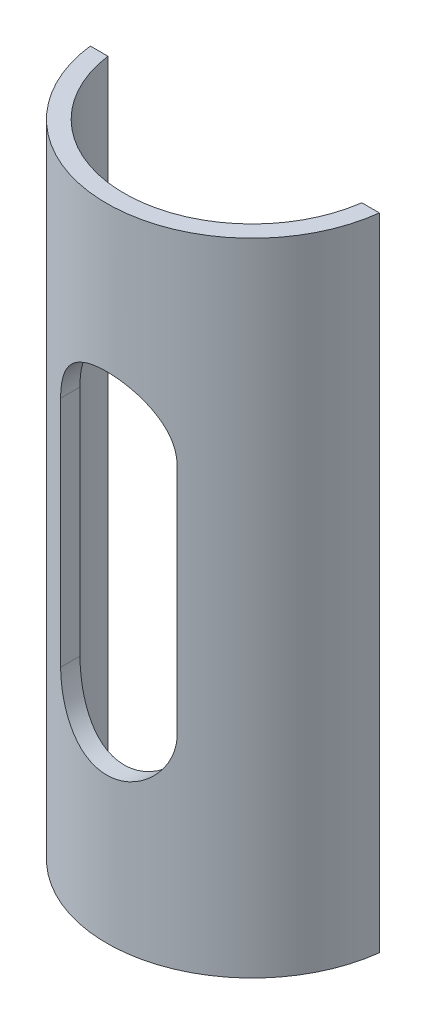
SolidWorks part; units mm, degrees
material "ASTM A36 Acier"
ref_plane "Front Plane" through (0, 0, 0) normal (0, 0, 1) x (1, 0, 0)
ref_plane "Top Plane" through (0, 0, 0) normal (0, 1, 0) x (1, 0, 0)
ref_plane "Right Plane" through (0, 0, 0) normal (1, 0, 0) x (0, 0, -1)
sketch "Sketch1" plane through (0, 0, 0) normal (0, 1, 0) x (1, 0, 0)
  line L0 (-24.8193, 3) -> (-21.7945, 3)
  line L1 (-24.8193, -3) -> (-21.7945, -3)
  line L2 (21.7945, 3) -> (24.8193, 3)
  line L3 (21.7945, -3) -> (24.8193, -3)
  arc A0 (-24.8193, -3) -> (24.8193, -3) centre (0, 0) ccw
  arc A1 (-21.7945, -3) -> (21.7945, -3) centre (0, 0) ccw
  arc A2 (21.7945, 3) -> (-21.7945, 3) centre (0, 0) ccw
  arc A3 (24.8193, 3) -> (-24.8193, 3) centre (0, 0) ccw
  dimension "D3" = 22
  dimension "D4" = 25
  dimension "D1" = 6
  dimension "D2" = 3
extrude "Boss-Extrude1" add sketch "Sketch1" along normal mid plane 110 contours A0 L3 A1 L1
sketch "Sketch2" plane through (0, 0, 0) normal (0, 0, 1) x (1, 0, 0)
  line L2 (-10, -20) -> (-10, 20)
  line L4 (10, -20) -> (10, 20)
  line L5 (-10, -20) -> (10, 20) construction
  line L6 (-10, 20) -> (10, -20) construction
  arc A0 (10, 20) -> (-10, 20) centre (0, 20) ccw
  arc A1 (-10, -20) -> (10, -20) centre (0, -20) ccw
  point P11 (0, 0)
  dimension "D3" = 10
  dimension "D1" = 20
  dimension "D2" = 40
extrude "Cut-Extrude1" cut sketch "Sketch2" along normal blind 80
